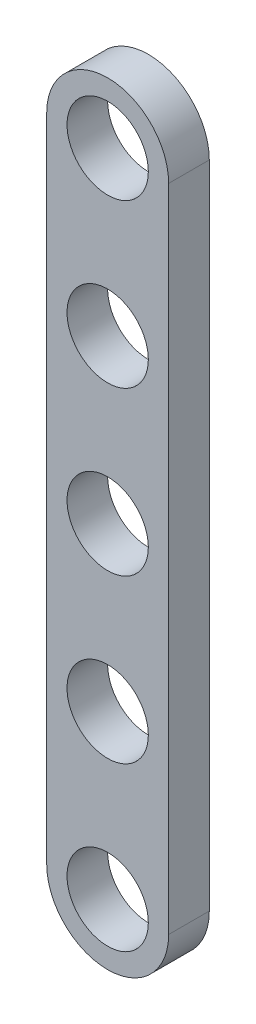
SolidWorks part; units mm, degrees
ref_plane "前视基准面" through (0, 0, 0) normal (0, 0, 1) x (1, 0, 0)
ref_plane "上视基准面" through (0, 0, 0) normal (0, 1, 0) x (1, 0, 0)
ref_plane "右视基准面" through (0, 0, 0) normal (1, 0, 0) x (0, 0, -1)
sketch "草图1" plane through (0, 0, 0) normal (0, 0, 1) x (1, 0, 0)
  line L0 (0, 0) -> (0, 16) construction
  line L1 (-1.5, 0) -> (-1.5, 16)
  line L2 (1.5, 0) -> (1.5, 16)
  arc A0 (-1.5, 0) -> (1.5, 0) centre (0, 0) ccw
  arc A1 (1.5, 16) -> (-1.5, 16) centre (0, 16) ccw
  circle A2 centre (0, 16) radius 1
  circle A3 centre (0, 8) radius 1
  circle A4 centre (0, 12) radius 1
  circle A5 centre (0, 0) radius 1
  circle A6 centre (0, 4) radius 1
  point P3 (0, 8)
  dimension "D1" = 1.5
  dimension "D3" = 2
  dimension "D4" = 4
  dimension "D2" = 16
  dimension "D5" = 4
extrude "凸台-拉伸1" add sketch "草图1" along normal blind 1
